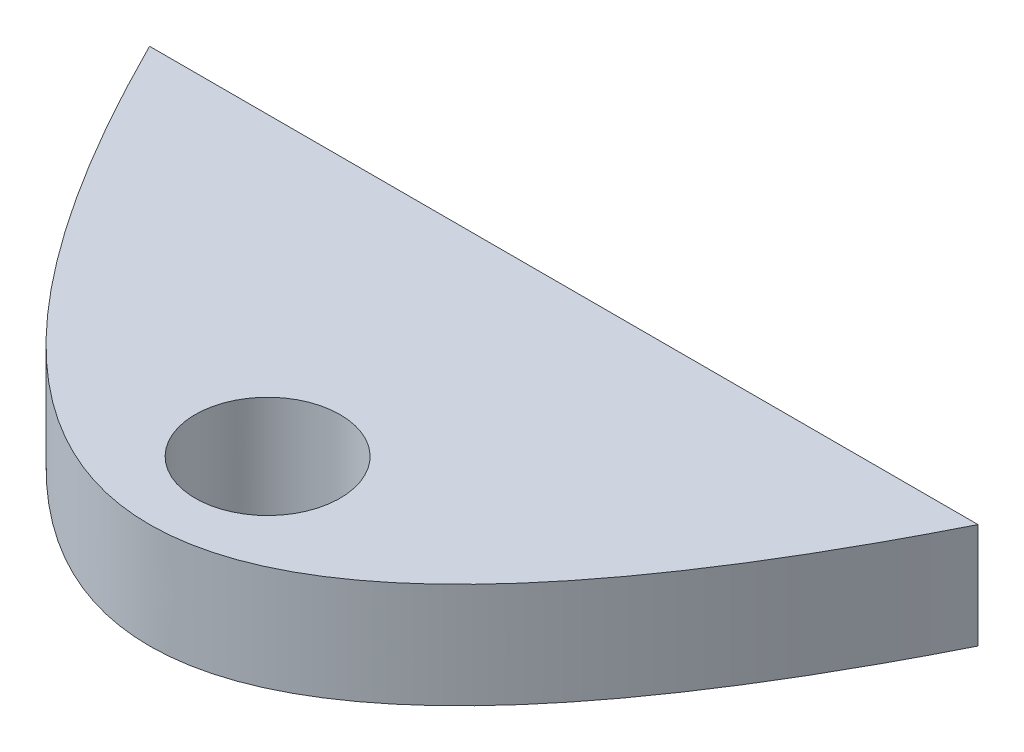
SolidWorks part; units mm, degrees
material "Custom Plastic (2)"
ref_plane "Front Plane" through (0, 0, 0) normal (0, 0, 1) x (1, 0, 0)
ref_plane "Top Plane" through (0, 0, 0) normal (0, 1, 0) x (1, 0, 0)
ref_plane "Right Plane" through (0, 0, 0) normal (1, 0, 0) x (0, 0, -1)
sketch "Sketch1" plane through (0, 0, 0) normal (0, 1, 0) x (1, 0, 0)
  line L0 (-200, 0) -> (200, 0)
  spline S0 degree 2 poles (-225.2396, 53.6645) (0, -453.6645) (225.2396, 53.6645) knots 0 0 0 1 1 1 construction
  spline S1 degree 2 poles (-200, 0) (0, -400) (200, 0) knots 0.056028 0.056028 0.056028 0.943972 0.943972 0.943972
extrude "Boss-Extrude1" add sketch "Sketch1" along normal blind 300
sketch "Sketch2" plane through (0, 300, 0) normal (0, 1, 0) x (1, 0, 0)
  line L0 (0, 200) -> (0, -200)
  line L2 (200, 0) -> (-200, 0) construction
  circle A0 centre (0, -143) radius 35
  parabola Q0 (-200, 0) -> (200, 0) focus (0, -150) apex (0, -200) construction
  point P4 (0, 0)
  dimension "D1" = 70
  dimension "D2" = 143
ref_plane "Plane1" through (0, 150, 0) normal (0, 1, 0) x (1, 0, 0)
sketch "Sketch3" plane through (0, 150, 0) normal (0, 1, 0) x (1, 0, 0)
  circle A0 centre (0, -143) radius 15.5
  dimension "D1" = 31
extrude "Cut-Extrude1" cut sketch "Sketch3" against normal blind 23 and the other way blind 23
ref_plane "Plane2" through (0, 173, 0) normal (0, 1, 0) x (1, 0, 0)
sketch "Sketch4" plane through (0, 173, 0) normal (0, 1, 0) x (1, 0, 0)
  circle A0 centre (0, -143) radius 35
extrude "Cut-Extrude3" cut sketch "Sketch4" along normal blind 300 contours A0
mirror "Mirror1" about plane through (0, 150, 0) normal (0, 1, 0) of "Cut-Extrude3"
sketch "Sketch5" plane through (0, 0, 0) normal (0, 0, -1) x (-1, 0, 0)
  line L0 (-200, 300) -> (200, 300) construction
  line L1 (-256.7983, 249.2) -> (266.9905, 249.2)
  line L2 (-256.7983, 249.2) -> (-256.7983, -14.9101)
  line L3 (-256.7983, -14.9101) -> (266.9905, -14.9101)
  line L4 (266.9905, 249.2) -> (266.9905, -14.9101)
  dimension "D1" = 50.8
extrude "Cut-Extrude4" cut sketch "Sketch5" against normal blind 300
